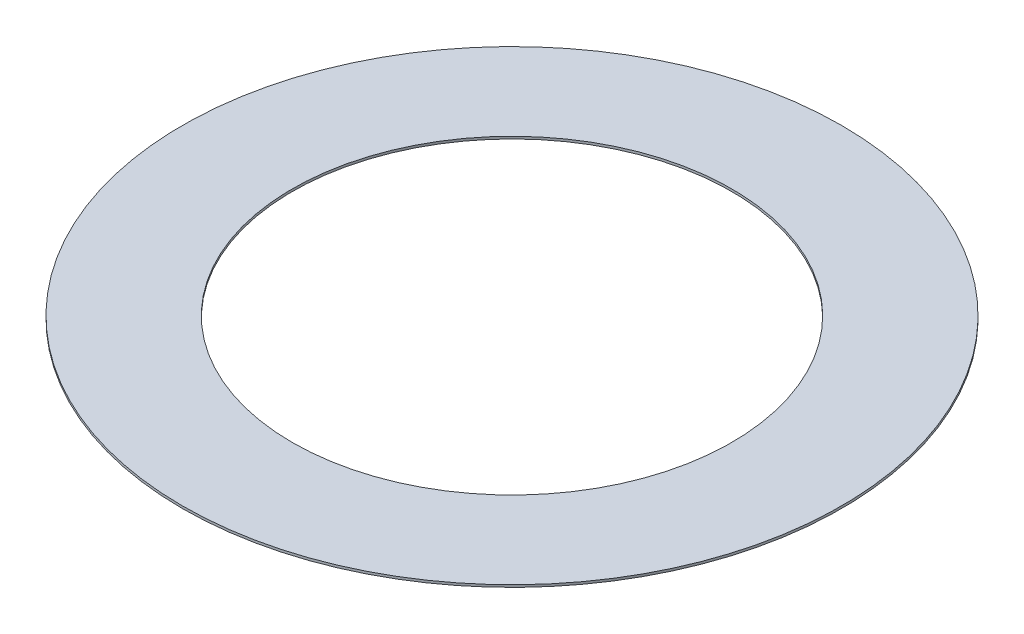
SolidWorks part; units mm, degrees
ref_plane "Front Plane" through (0, 0, 0) normal (0, 0, 1) x (1, 0, 0)
ref_plane "Top Plane" through (0, 0, 0) normal (0, 1, 0) x (1, 0, 0)
ref_plane "Right Plane" through (0, 0, 0) normal (1, 0, 0) x (0, 0, -1)
sketch "Sketch1" plane through (0, 0, 0) normal (0, 1, 0) x (1, 0, 0)
  circle A0 centre (0, 0) radius 14.2875
  dimension "OD" = 28.575
extrude "Boss-Extrude1" add sketch "Sketch1" along normal blind 0.1016
sketch "Sketch5" plane through (0, 0.1016, 0) normal (0, 1, 0) x (-1, 0, 0)
  circle A0 centre (0, 0) radius 9.525
  dimension "ID" = 19.05
extrude "Cut-Extrude1" cut sketch "Sketch5" against normal through all
